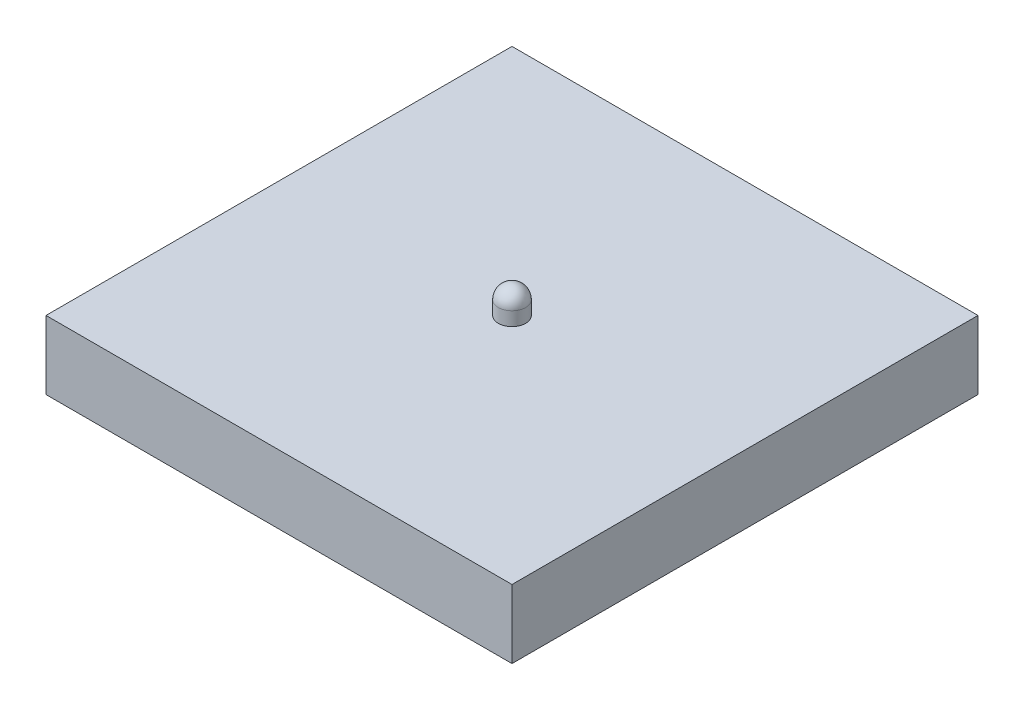
SolidWorks part; units mm, degrees
ref_plane "Front Plane" through (0, 0, 0) normal (0, 0, 1) x (1, 0, 0)
ref_plane "Top Plane" through (0, 0, 0) normal (0, 1, 0) x (1, 0, 0)
ref_plane "Right Plane" through (0, 0, 0) normal (1, 0, 0) x (0, 0, -1)
sketch "Sketch2" plane through (0, 0, 0) normal (0, 1, 0) x (1, 0, 0)
  line L1 (-17, -17) -> (17, -17)
  line L2 (-17, -17) -> (-17, 17)
  line L3 (-17, 17) -> (17, 17)
  line L4 (17, -17) -> (17, 17)
  line L5 (-17, -17) -> (17, 17) construction
  line L6 (-17, 17) -> (17, -17) construction
  point P0 (0, 0)
  dimension "D1" = 34
  dimension "D2" = 34
extrude "Boss-Extrude1" add sketch "Sketch2" along normal blind 5
sketch "Sketch3" plane through (0, 0, 0) normal (0, -1, 0) x (1, 0, 0)
  line L1 (-16, -16) -> (16, -16)
  line L2 (-16, -16) -> (-16, 16)
  line L3 (-16, 16) -> (16, 16)
  line L4 (16, -16) -> (16, 16)
  line L5 (-16, -16) -> (16, 16) construction
  line L6 (-16, 16) -> (16, -16) construction
  point P0 (0, 0)
  dimension "D1" = 32
  dimension "D2" = 32
extrude "Cut-Extrude1" cut sketch "Sketch3" against normal blind 3
sketch "Sketch4" plane through (0, 5, 0) normal (0, 1, 0) x (1, 0, 0)
  circle A0 centre (0, 0) radius 1
  dimension "D1" = 2
extrude "Boss-Extrude2" add sketch "Sketch4" along normal blind 2
fillet "Fillet1" radius 1 1 edges at (0, 7, 1)
